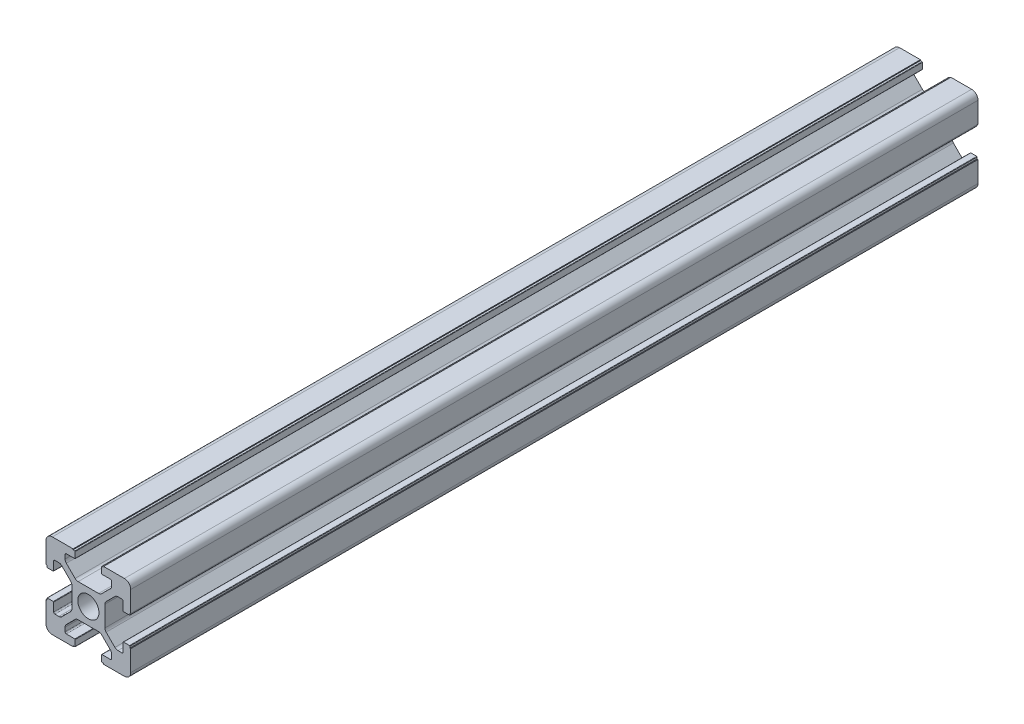
SolidWorks part; units mm, degrees
material "6063-T5"
ref_plane "前视基准面" through (0, 0, 0) normal (0, 0, 1) x (1, 0, 0)
ref_plane "上视基准面" through (0, 0, 0) normal (0, 1, 0) x (1, 0, 0)
ref_plane "右视基准面" through (0, 0, 0) normal (1, 0, 0) x (0, 0, -1)
sketch "草图1" plane through (0, 0, 0) normal (0, 0, 1) x (1, 0, 0)
  line L0 (-1.4389, 10) -> (24.3741, 10) construction
  line L1 (20, 13.6) -> (20, 20)
  line L2 (0, 0) -> (0, 6.4)
  line L3 (0, 20) -> (6.4, 20)
  line L4 (20, 0) -> (20, 6.4)
  line L5 (10, 21.5388) -> (10, -2.4017) construction
  line L6 (6.9, 18.3) -> (6.9, 19.7)
  line L7 (6.8, 18.2) -> (4.8, 18.2)
  line L8 (4.5, 17.9) -> (4.5, 16.9749)
  line L9 (4.7929, 16.2678) -> (6.8678, 14.1929)
  line L10 (7.5749, 13.9) -> (12.4251, 13.9)
  line L11 (6.8, 19.8) -> (6.4, 19.8)
  line L12 (6.4, 19.8) -> (6.4, 20)
  line L13 (0, 13.6) -> (0.2, 13.6)
  line L14 (0.2, 13.6) -> (0.2, 13.2)
  line L15 (0.3, 13.1) -> (1.7, 13.1)
  line L16 (1.8, 13.2) -> (1.8, 15.2)
  line L17 (2.1, 15.5) -> (3.0251, 15.5)
  line L18 (3.7322, 15.2071) -> (5.8071, 13.1322)
  line L19 (6.1, 12.4251) -> (6.1, 7.5749)
  line L20 (13.6, 19.8) -> (13.6, 20)
  line L21 (13.2, 19.8) -> (13.6, 19.8)
  line L22 (13.1, 18.3) -> (13.1, 19.7)
  line L23 (13.2, 18.2) -> (15.2, 18.2)
  line L24 (15.5, 17.9) -> (15.5, 16.9749)
  line L25 (15.2071, 16.2678) -> (13.1322, 14.1929)
  line L26 (0, 6.4) -> (0.2, 6.4)
  line L27 (0.2, 6.4) -> (0.2, 6.8)
  line L28 (0.3, 6.9) -> (1.7, 6.9)
  line L29 (1.8, 6.8) -> (1.8, 4.8)
  line L30 (2.1, 4.5) -> (3.0251, 4.5)
  line L31 (3.7322, 4.7929) -> (5.8071, 6.8678)
  line L32 (13.6, 20) -> (20, 20)
  line L33 (0, 13.6) -> (0, 20)
  line L34 (13.6, 0.2) -> (13.6, 0)
  line L35 (13.2, 0.2) -> (13.6, 0.2)
  line L36 (13.1, 1.7) -> (13.1, 0.3)
  line L37 (13.2, 1.8) -> (15.2, 1.8)
  line L38 (15.5, 2.1) -> (15.5, 3.0251)
  line L39 (15.2071, 3.7322) -> (13.1322, 5.8071)
  line L40 (4.5, 2.1) -> (4.5, 3.0251)
  line L41 (6.8, 1.8) -> (4.8, 1.8)
  line L42 (6.4, 0.2) -> (6.4, 0)
  line L43 (6.8, 0.2) -> (6.4, 0.2)
  line L44 (6.9, 1.7) -> (6.9, 0.3)
  line L45 (4.7929, 3.7322) -> (6.8678, 5.8071)
  line L46 (7.5749, 6.1) -> (12.4251, 6.1)
  line L47 (20, 6.4) -> (19.8, 6.4)
  line L48 (19.8, 6.4) -> (19.8, 6.8)
  line L49 (19.7, 6.9) -> (18.3, 6.9)
  line L50 (18.2, 6.8) -> (18.2, 4.8)
  line L51 (17.9, 4.5) -> (16.9749, 4.5)
  line L52 (16.2678, 4.7929) -> (14.1929, 6.8678)
  line L53 (13.9, 12.4251) -> (13.9, 7.5749)
  line L54 (16.2678, 15.2071) -> (14.1929, 13.1322)
  line L55 (17.9, 15.5) -> (16.9749, 15.5)
  line L56 (18.2, 13.2) -> (18.2, 15.2)
  line L57 (19.7, 13.1) -> (18.3, 13.1)
  line L58 (19.8, 13.6) -> (19.8, 13.2)
  line L59 (20, 13.6) -> (19.8, 13.6)
  line L60 (0, 0) -> (6.4, 0)
  line L61 (13.6, 0) -> (20, 0)
  arc A0 (6.1, 12.4251) -> (5.8071, 13.1322) centre (5.1, 12.4251) ccw
  arc A1 (7.5749, 13.9) -> (6.8678, 14.1929) centre (7.5749, 14.9) cw
  arc A2 (4.5, 16.9749) -> (4.7929, 16.2678) centre (5.5, 16.9749) ccw
  arc A3 (3.7322, 15.2071) -> (3.0251, 15.5) centre (3.0251, 14.5) ccw
  arc A4 (4.5, 17.9) -> (4.8, 18.2) centre (4.8, 17.9) cw
  arc A5 (1.8, 15.2) -> (2.1, 15.5) centre (2.1, 15.2) cw
  arc A6 (0.3, 13.1) -> (0.2, 13.2) centre (0.3, 13.2) cw
  arc A7 (6.9, 19.7) -> (6.8, 19.8) centre (6.8, 19.7) ccw
  arc A8 (1.7, 13.1) -> (1.8, 13.2) centre (1.7, 13.2) ccw
  arc A9 (6.9, 18.3) -> (6.8, 18.2) centre (6.8, 18.3) cw
  arc A10 (13.1, 19.7) -> (13.2, 19.8) centre (13.2, 19.7) cw
  arc A11 (13.1, 18.3) -> (13.2, 18.2) centre (13.2, 18.3) ccw
  arc A12 (15.5, 17.9) -> (15.2, 18.2) centre (15.2, 17.9) ccw
  arc A13 (15.5, 16.9749) -> (15.2071, 16.2678) centre (14.5, 16.9749) cw
  arc A14 (12.4251, 13.9) -> (13.1322, 14.1929) centre (12.4251, 14.9) ccw
  arc A15 (0.3, 6.9) -> (0.2, 6.8) centre (0.3, 6.8) ccw
  arc A16 (1.7, 6.9) -> (1.8, 6.8) centre (1.7, 6.8) cw
  arc A17 (1.8, 4.8) -> (2.1, 4.5) centre (2.1, 4.8) ccw
  arc A18 (3.7322, 4.7929) -> (3.0251, 4.5) centre (3.0251, 5.5) cw
  arc A19 (6.1, 7.5749) -> (5.8071, 6.8678) centre (5.1, 7.5749) cw
  arc A20 (13.1, 0.3) -> (13.2, 0.2) centre (13.2, 0.3) ccw
  arc A21 (13.1, 1.7) -> (13.2, 1.8) centre (13.2, 1.7) cw
  arc A22 (15.5, 2.1) -> (15.2, 1.8) centre (15.2, 2.1) cw
  arc A23 (15.5, 3.0251) -> (15.2071, 3.7322) centre (14.5, 3.0251) ccw
  arc A24 (12.4251, 6.1) -> (13.1322, 5.8071) centre (12.4251, 5.1) cw
  arc A25 (4.5, 2.1) -> (4.8, 1.8) centre (4.8, 2.1) ccw
  arc A26 (6.9, 0.3) -> (6.8, 0.2) centre (6.8, 0.3) cw
  arc A27 (6.9, 1.7) -> (6.8, 1.8) centre (6.8, 1.7) ccw
  arc A28 (4.5, 3.0251) -> (4.7929, 3.7322) centre (5.5, 3.0251) cw
  arc A29 (7.5749, 6.1) -> (6.8678, 5.8071) centre (7.5749, 5.1) ccw
  arc A30 (19.7, 6.9) -> (19.8, 6.8) centre (19.7, 6.8) cw
  arc A31 (18.3, 6.9) -> (18.2, 6.8) centre (18.3, 6.8) ccw
  arc A32 (18.2, 4.8) -> (17.9, 4.5) centre (17.9, 4.8) cw
  arc A33 (16.2678, 4.7929) -> (16.9749, 4.5) centre (16.9749, 5.5) ccw
  arc A34 (13.9, 7.5749) -> (14.1929, 6.8678) centre (14.9, 7.5749) ccw
  arc A35 (13.9, 12.4251) -> (14.1929, 13.1322) centre (14.9, 12.4251) cw
  arc A36 (16.2678, 15.2071) -> (16.9749, 15.5) centre (16.9749, 14.5) cw
  arc A37 (18.2, 15.2) -> (17.9, 15.5) centre (17.9, 15.2) ccw
  arc A38 (18.3, 13.1) -> (18.2, 13.2) centre (18.3, 13.2) cw
  arc A39 (19.7, 13.1) -> (19.8, 13.2) centre (19.7, 13.2) ccw
  circle A40 centre (10, 10) radius 2.5
  point P39 (0.2, 13.1)
  point P42 (6.9, 19.8)
  point P45 (1.8, 13.1)
  point P48 (6.9, 18.2)
  point P66 (10, 13.9)
  point P83 (6.1, 10)
  dimension "D19" = 1
  dimension "D20" = 1
  dimension "D21" = 0.3
  dimension "D22" = 0.1
  dimension "D23" = 5
  dimension "D1" = 20
  dimension "D2" = 20
  dimension "D3" = 10
  dimension "D4" = 10
  dimension "D5" = 1.8
  dimension "D6" = 0.5
  dimension "D7" = 1.6
  dimension "D8" = 3.1
  dimension "D9" = 6.1
  dimension "D10" = 5.5
  dimension "D11" = 3.1
  dimension "D12" = 6.1
  dimension "D13" = 5.5
  dimension "D14" = 1.8
  dimension "D15" = 0.5
  dimension "D16" = 1.5
  dimension "D17" = 45
  dimension "D18" = 1.6
extrude "凸台-拉伸1" add sketch "草图1" along normal blind 200
fillet "圆角1" radius 1.5 4 edges at (20, 0, 100) (0, 0, 100) (0, 20, 100) (20, 20, 100)
